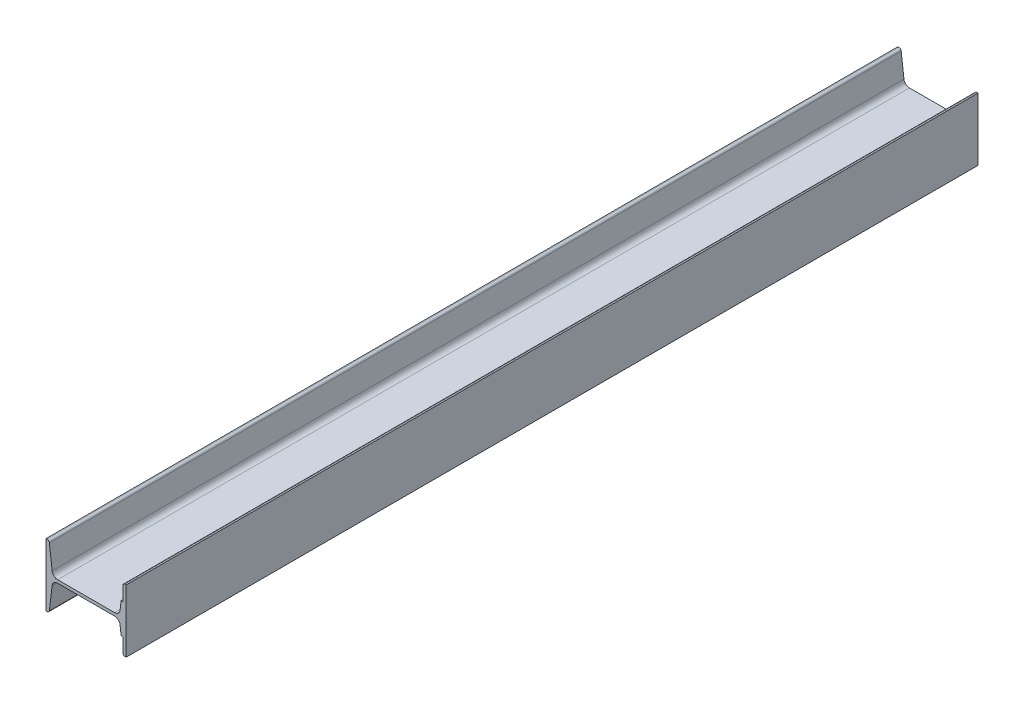
SolidWorks part; units mm, degrees
ref_plane "Front Plane" through (0, 0, 0) normal (0, 0, 1) x (1, 0, 0)
ref_plane "Top Plane" through (0, 0, 0) normal (0, 1, 0) x (1, 0, 0)
ref_plane "Right Plane" through (0, 0, 0) normal (1, 0, 0) x (0, 0, -1)
ref_plane "Plane1" through (0, 0, 1800) normal (0, 0, 1) x (1, 0, 0)
sketch "Sketch1" plane through (0, 0, 1800) normal (0, 0, 1) x (1, 0, 0)
  line L0 (129, 60.4688) -> (129, 30)
  line L1 (129, 30) -> (124.9197, 30)
  line L2 (124.9197, 30) -> (122.7927, 12.6894)
  line L3 (111.8711, 3) -> (-1.8711, 3)
  line L4 (-12.7927, 12.6894) -> (-18.2943, 58.5362)
  line L5 (-22.7623, 62.5) -> (-25, 62.5)
  line L6 (-25, 62.5) -> (-25, -62.5)
  line L7 (-25, -62.5) -> (-22.7623, -62.5)
  line L8 (-18.2943, -58.5362) -> (-12.7927, -12.6894)
  line L9 (-1.8711, -3) -> (111.8711, -3)
  line L10 (122.7927, -12.6894) -> (124.87, -30)
  line L11 (124.87, -30) -> (129, -30)
  line L12 (129, -30) -> (129, -60.4688)
  line L13 (132.7623, -62.5) -> (135, -62.5)
  line L14 (135, -62.5) -> (135, 62.5)
  line L15 (135, 62.5) -> (132.7623, 62.5)
  arc A0 (122.7927, 12.6894) -> (111.8711, 3) centre (111.8711, 14) cw
  arc A1 (-1.8711, 3) -> (-12.7927, 12.6894) centre (-1.8711, 14) cw
  arc A2 (-18.2943, 58.5362) -> (-22.7623, 62.5) centre (-22.7623, 58) ccw
  arc A3 (-22.7623, -62.5) -> (-18.2943, -58.5362) centre (-22.7623, -58) ccw
  arc A4 (-12.7927, -12.6894) -> (-1.8711, -3) centre (-1.8711, -14) cw
  arc A5 (111.8711, -3) -> (122.7927, -12.6894) centre (111.8711, -14) cw
  arc A6 (129, -60.4688) -> (132.7623, -62.5) centre (132.7623, -58) ccw
  arc A7 (132.7623, 62.5) -> (129, 60.4688) centre (132.7623, 58) ccw
extrude "Boss-Extrude1" add sketch "Sketch1" against normal blind 1700
scale "Scale1" scale about centroid uniform scaling yes scale factor 0.75
sketch "Sketch2" plane through (0, 0, 312.5) normal (0, 0, -1) x (-1, 0, 0)
